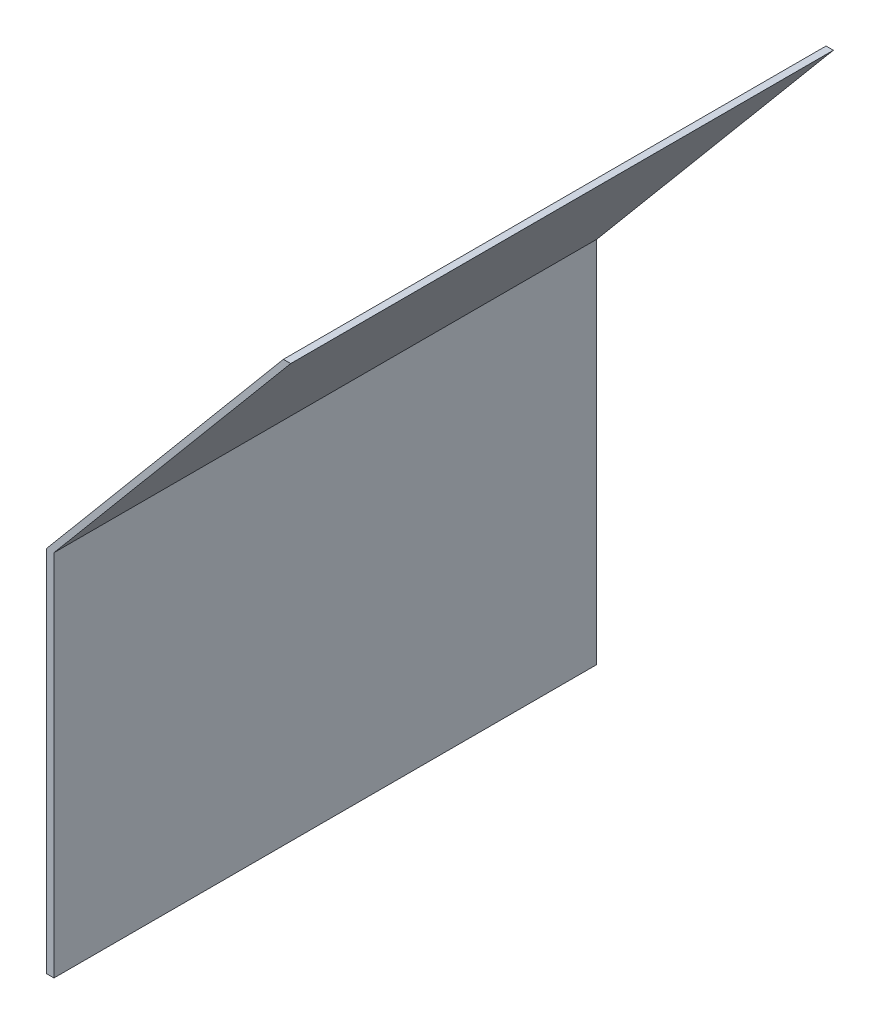
SolidWorks part; units mm, degrees
material "Plain Carbon Steel"
ref_plane "Front Plane" through (0, 0, 0) normal (0, 0, 1) x (1, 0, 0)
ref_plane "Top Plane" through (0, 0, 0) normal (0, 1, 0) x (1, 0, 0)
ref_plane "Right Plane" through (0, 0, 0) normal (1, 0, 0) x (0, 0, -1)
sketch "Sketch1" plane through (0, 0, 0) normal (0, 0, 1) x (1, 0, 0)
  line L0 (0, 0) -> (1.5189, 0)
  line L1 (1.5189, 0) -> (1.5189, 76.2)
  line L2 (1.5189, 76.2) -> (50.4993, 134.5726)
  line L3 (50.4993, 134.5726) -> (48.9804, 134.5726)
  line L4 (48.9804, 134.5726) -> (0, 76.2)
  line L5 (0, 76.2) -> (0, 0)
  dimension "D1" = 1.5189
  dimension "D2" = 1.5189
  dimension "D3" = 76.2
  dimension "D4" = 76.2
  dimension "D5" = 140
extrude "Boss-Extrude1" add sketch "Sketch1" along normal blind 112.268
